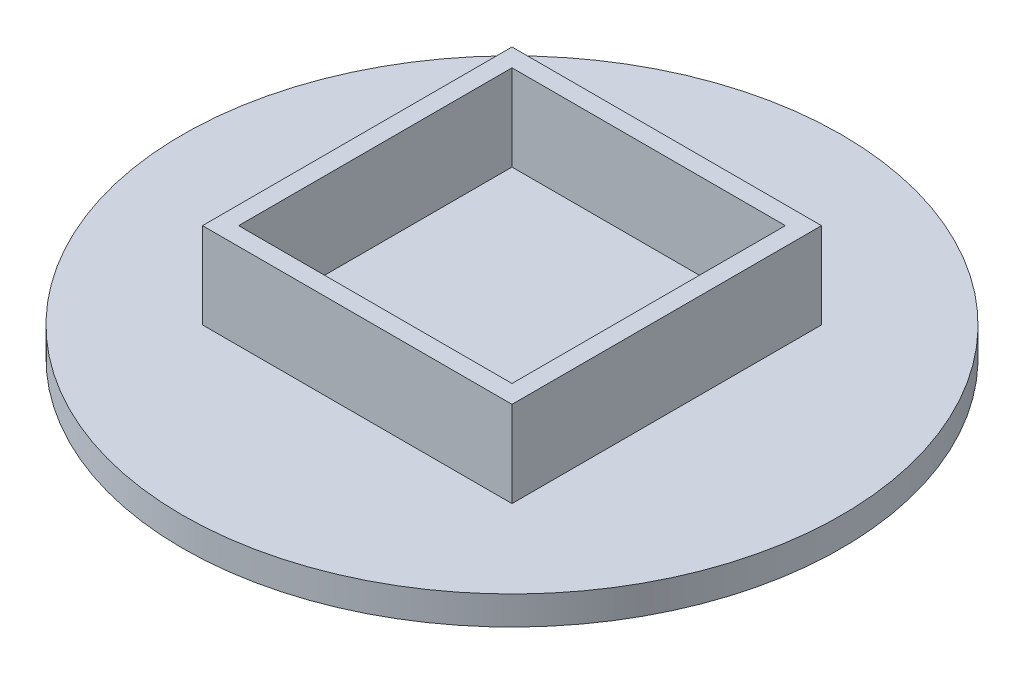
SolidWorks part; units mm, degrees
material "ABS_rapid_prototype"
ref_plane "Front" through (0, 0, 0) normal (0, 0, 1) x (1, 0, 0)
ref_plane "Top" through (0, 0, 0) normal (0, 1, 0) x (1, 0, 0)
ref_plane "Right" through (0, 0, 0) normal (1, 0, 0) x (0, 0, -1)
sketch "Sketch1" plane through (0, 0, 0) normal (0, 1, 0) x (1, 0, 0)
  line L1 (-50.8, 50.8) -> (50.8, 50.8)
  line L2 (-50.8, 50.8) -> (-50.8, -50.8)
  line L3 (-50.8, -50.8) -> (50.8, -50.8)
  line L4 (50.8, 50.8) -> (50.8, -50.8)
  line L5 (-50.8, 50.8) -> (50.8, -50.8) construction
  line L6 (-50.8, -50.8) -> (50.8, 50.8) construction
  line L7 (-38.1, 38.1) -> (38.1, 38.1)
  line L8 (-38.1, 38.1) -> (-38.1, -38.1)
  line L9 (-38.1, -38.1) -> (38.1, -38.1)
  line L10 (38.1, 38.1) -> (38.1, -38.1)
  line L11 (-38.1, 38.1) -> (38.1, -38.1) construction
  line L12 (-38.1, -38.1) -> (38.1, 38.1) construction
  line L13 (-34.29, 34.29) -> (34.29, 34.29)
  line L14 (-34.29, 34.29) -> (-34.29, -34.29)
  line L15 (-34.29, -34.29) -> (34.29, -34.29)
  line L16 (34.29, 34.29) -> (34.29, -34.29)
  line L17 (-34.29, 34.29) -> (34.29, -34.29) construction
  line L18 (-34.29, -34.29) -> (34.29, 34.29) construction
  line L19 (-30.29, 30.29) -> (30.29, 30.29)
  line L20 (-30.29, 30.29) -> (-30.29, -30.29)
  line L21 (-30.29, -30.29) -> (30.29, -30.29)
  line L22 (30.29, 30.29) -> (30.29, -30.29)
  line L23 (-30.29, 30.29) -> (30.29, -30.29) construction
  line L24 (-30.29, -30.29) -> (30.29, 30.29) construction
  point P0 (0, 0)
  point P5 (0, 0)
  point P11 (0, 0)
  point P16 (0, 0)
  dimension "D1" = 101.6
  dimension "D2" = 76.2
  dimension "D3" = 68.58
  dimension "D4" = 60.58
extrude "Boss-Extrude1" add sketch "Sketch1" along normal blind 25.4 contours L16 L13 L14 L15 L19 L22 L21 L20
sketch "Sketch2" plane through (0, 0, 0) normal (0, 1, 0) x (1, 0, 0)
  line L7 (-34.29, -34.29) -> (34.29, -34.29)
  line L8 (-34.29, -34.29) -> (-34.29, 34.29)
  line L9 (-34.29, 34.29) -> (34.29, 34.29)
  line L10 (34.29, -34.29) -> (34.29, 34.29)
  circle A0 centre (0, 0) radius 73.025
  point P0 (0, 0)
  point P5 (0, 0)
  dimension "D1" = 146.05
extrude "Boss-Extrude2" add sketch "Sketch2" along normal blind 6.35 contours A0
